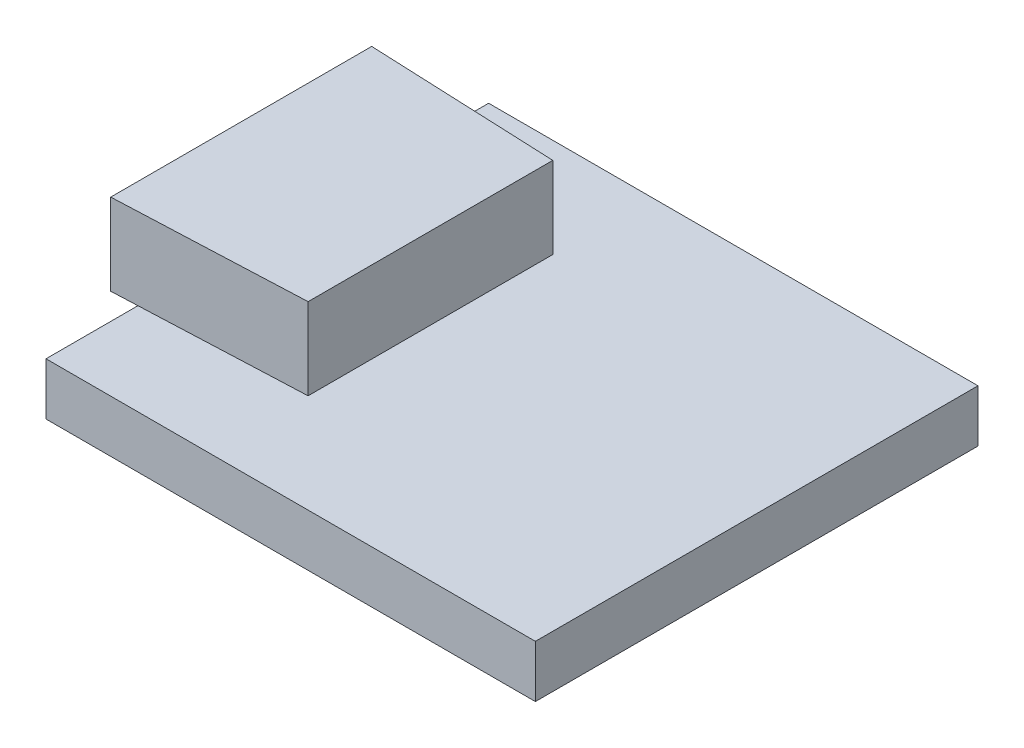
SolidWorks part; units mm, degrees
ref_plane "前视基准面" through (0, 0, 0) normal (0, 0, 1) x (1, 0, 0)
ref_plane "上视基准面" through (0, 0, 0) normal (0, 1, 0) x (1, 0, 0)
ref_plane "右视基准面" through (0, 0, 0) normal (1, 0, 0) x (0, 0, -1)
sketch "草图1" plane through (0, 0, 0) normal (0, 1, 0) x (1, 0, 0)
  line L1 (-7.5, -6.7833) -> (7.5, -6.7833)
  line L2 (-7.5, -6.7833) -> (-7.5, 6.7833)
  line L3 (-7.5, 6.7833) -> (7.5, 6.7833)
  line L4 (7.5, -6.7833) -> (7.5, 6.7833)
  line L5 (-7.5, -6.7833) -> (7.5, 6.7833) construction
  line L6 (-7.5, 6.7833) -> (7.5, -6.7833) construction
  point P0 (0, 0)
  dimension "D1" = 15
  dimension "D2" = 13.5667
extrude "凸台-拉伸1" add sketch "草图1" along normal blind 1.6
sketch "草图2" plane through (0, 1.6, 0) normal (0, 1, 0) x (1, 0, 0)
  line L0 (0, 0) -> (-7.5, 0) construction
  line L1 (-7.5, 6.7833) -> (-7.5, -6.7833) construction
  line L2 (-8.3, -4) -> (-8.3, 4)
  line L7 (-8.3, 4) -> (-2.5, 3.75)
  line L8 (-2.5, 3.75) -> (-2.5, -3.75)
  line L9 (-8.3, -4) -> (-2.5, -3.75)
  point P10 (-2.5, 0)
  point P11 (-8.3, 0)
  dimension "D1" = 7.5
  dimension "D2" = 8
  dimension "D3" = 5.8
  dimension "D4" = 0.8
extrude "凸台-拉伸2" add sketch "草图2" along normal blind 2.5
